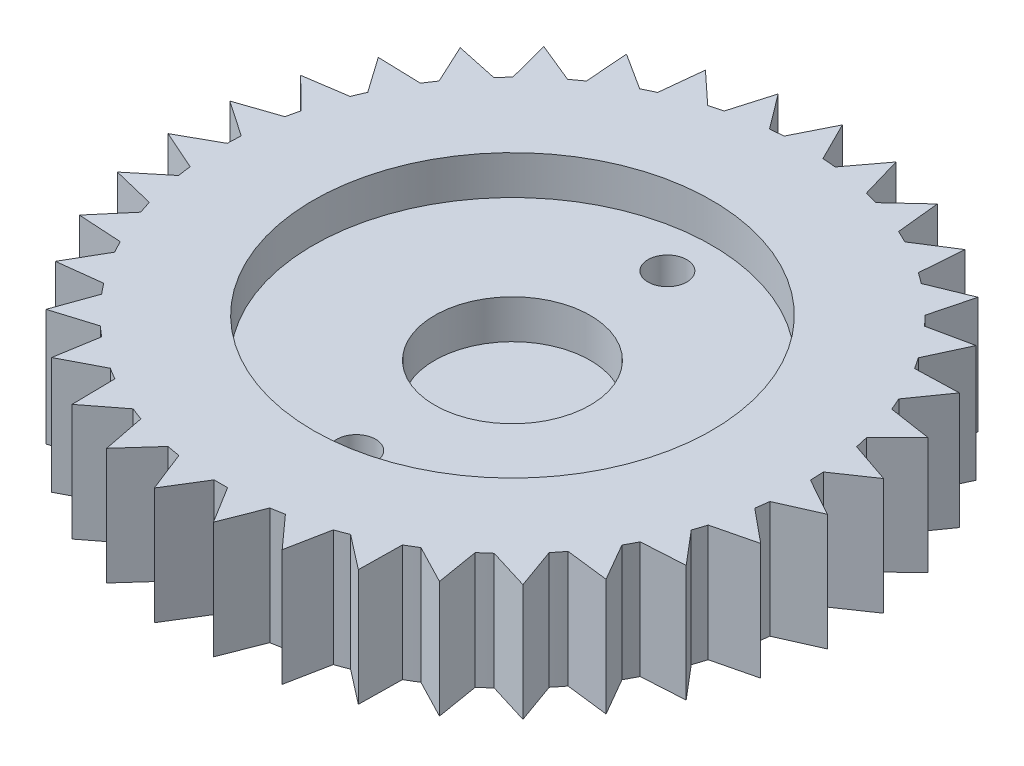
SolidWorks part; units mm, degrees
ref_plane "前视基准面" through (0, 0, 0) normal (0, 0, 1) x (1, 0, 0)
ref_plane "上视基准面" through (0, 0, 0) normal (0, 1, 0) x (1, 0, 0)
ref_plane "右视基准面" through (0, 0, 0) normal (1, 0, 0) x (0, 0, -1)
sketch "草图1" plane through (0, 0, 0) normal (0, 1, 0) x (1, 0, 0)
  circle A0 centre (0, 0) radius 15
  dimension "D1" = 30
extrude "凸台-拉伸1" add sketch "草图1" along normal blind 6
sketch "草图2" plane through (0, 6, 0) normal (0, 1, 0) x (1, 0, 0)
  line L0 (0, 16.9666) -> (-1, 14.9666)
  line L2 (1, 14.9666) -> (0, 16.9666)
  line L3 (0, 18.4375) -> (0, 11.2196) construction
  line L4 (-1, 14.9666) -> (-1, 14.9408)
  line L5 (-1, 14.9408) -> (1, 14.9408)
  line L6 (1, 14.9408) -> (1, 14.9666)
  line L7 (3.6563, 14.5476) -> (3.0295, 16.694)
  line L8 (3.0295, 16.694) -> (1.6885, 14.9047)
  line L9 (1.6885, 14.9047) -> (1.6838, 14.8792)
  line L10 (3.6517, 14.5221) -> (3.6563, 14.5476)
  line L11 (1.6838, 14.8792) -> (3.6517, 14.5221)
  line L12 (6.1951, 13.6609) -> (5.9616, 15.8848)
  line L13 (5.9616, 15.8848) -> (4.3227, 14.3637)
  line L14 (4.3227, 14.3637) -> (4.3136, 14.3394)
  line L15 (6.186, 13.6367) -> (6.1951, 13.6609)
  line L16 (4.3136, 14.3394) -> (6.186, 13.6367)
  line L17 (8.5348, 12.3352) -> (8.7022, 14.565)
  line L18 (8.7022, 14.565) -> (6.8179, 13.361)
  line L19 (6.8179, 13.361) -> (6.8047, 13.3388)
  line L20 (8.5216, 12.313) -> (8.5348, 12.3352)
  line L21 (6.8047, 13.3388) -> (8.5216, 12.313)
  line L22 (10.6002, 10.613) -> (11.163, 12.7771)
  line L23 (11.163, 12.7771) -> (9.0941, 11.9289)
  line L24 (9.0941, 11.9289) -> (9.077, 11.9094)
  line L25 (10.5832, 10.5935) -> (10.6002, 10.613)
  line L26 (9.077, 11.9094) -> (10.5832, 10.5935)
  line L27 (12.3249, 8.5497) -> (13.265, 10.5785)
  line L28 (13.265, 10.5785) -> (11.0779, 10.1134)
  line L29 (11.0779, 10.1134) -> (11.0577, 10.0973)
  line L30 (12.3047, 8.5336) -> (12.3249, 8.5497)
  line L31 (11.0577, 10.0973) -> (12.3047, 8.5336)
  line L32 (13.6534, 6.2116) -> (14.9407, 8.04)
  line L33 (14.9407, 8.04) -> (12.7057, 7.9728)
  line L34 (12.7057, 7.9728) -> (12.6829, 7.9606)
  line L35 (13.6306, 6.1994) -> (13.6534, 6.2116)
  line L36 (12.6829, 7.9606) -> (13.6306, 6.1994)
  line L37 (14.5431, 3.6739) -> (16.1362, 5.243)
  line L38 (16.1362, 5.243) -> (13.9251, 5.576)
  line L39 (13.9251, 5.576) -> (13.9005, 5.568)
  line L40 (14.5185, 3.6659) -> (14.5431, 3.6739)
  line L41 (13.9005, 5.568) -> (14.5185, 3.6659)
  line L42 (14.9654, 1.0181) -> (16.8131, 2.2775)
  line L43 (16.8131, 2.2775) -> (14.6969, 3)
  line L44 (14.6969, 3) -> (14.6713, 2.9965)
  line L45 (14.9398, 1.0146) -> (14.9654, 1.0181)
  line L46 (14.6713, 2.9965) -> (14.9398, 1.0146)
  line L47 (14.9067, -1.6705) -> (16.9495, -0.7612)
  line L48 (16.9495, -0.7612) -> (14.9964, 0.3275)
  line L49 (14.9964, 0.3275) -> (14.9706, 0.3287)
  line L50 (14.8809, -1.6693) -> (14.9067, -1.6705)
  line L51 (14.9706, 0.3287) -> (14.8809, -1.6693)
  line L52 (14.3689, -4.3053) -> (16.5412, -3.7754)
  line L53 (16.5412, -3.7754) -> (14.8139, -2.3555)
  line L54 (14.8139, -2.3555) -> (14.7887, -2.3497)
  line L55 (14.3437, -4.2996) -> (14.3689, -4.3053)
  line L56 (14.7887, -2.3497) -> (14.3437, -4.2996)
  line L57 (13.3692, -6.8018) -> (15.6013, -6.6683)
  line L58 (15.6013, -6.6683) -> (14.1553, -4.9627)
  line L59 (14.1553, -4.9627) -> (14.1315, -4.9526)
  line L60 (13.3454, -6.7916) -> (13.3692, -6.8018)
  line L61 (14.1315, -4.9526) -> (13.3454, -6.7916)
  line L62 (11.9399, -9.0796) -> (14.1599, -9.3469)
  line L63 (14.1599, -9.3469) -> (13.0416, -7.4105)
  line L64 (13.0416, -7.4105) -> (13.0201, -7.3963)
  line L65 (11.9183, -9.0654) -> (11.9399, -9.0796)
  line L66 (13.0201, -7.3963) -> (11.9183, -9.0654)
  line L67 (10.1267, -11.0657) -> (12.2634, -11.725)
  line L68 (12.2634, -11.725) -> (11.5089, -9.6201)
  line L69 (11.5089, -9.6201) -> (11.4902, -9.6022)
  line L70 (10.1081, -11.0478) -> (10.1267, -11.0657)
  line L71 (11.4902, -9.6022) -> (10.1081, -11.0478)
  line L72 (7.9881, -12.696) -> (9.9727, -13.7263)
  line L73 (9.9727, -13.7263) -> (9.6062, -11.5205)
  line L74 (9.6062, -11.5205) -> (9.591, -11.4996)
  line L75 (7.9729, -12.6751) -> (7.9881, -12.696)
  line L76 (9.591, -11.4996) -> (7.9729, -12.6751)
  line L77 (5.5928, -13.9184) -> (7.3615, -15.2864)
  line L78 (7.3615, -15.2864) -> (7.3947, -13.0506)
  line L79 (7.3947, -13.0506) -> (7.3835, -13.0273)
  line L80 (5.5816, -13.8951) -> (5.5928, -13.9184)
  line L81 (7.3835, -13.0273) -> (5.5816, -13.8951)
  line L82 (3.0177, -14.6933) -> (4.5137, -16.3552)
  line L83 (4.5137, -16.3552) -> (4.9456, -14.1612)
  line L84 (4.9456, -14.1612) -> (4.9388, -14.1363)
  line L85 (3.0108, -14.6684) -> (3.0177, -14.6933)
  line L86 (4.9388, -14.1363) -> (3.0108, -14.6684)
  line L87 (0.3456, -14.996) -> (1.5209, -16.8983)
  line L88 (1.5209, -16.8983) -> (2.3376, -14.8167)
  line L89 (2.3376, -14.8167) -> (2.3353, -14.791)
  line L90 (0.3433, -14.9703) -> (0.3456, -14.996)
  line L91 (2.3353, -14.791) -> (0.3433, -14.9703)
  line L92 (-2.3376, -14.8167) -> (-1.5209, -16.8983)
  line L93 (-1.5209, -16.8983) -> (-0.3456, -14.996)
  line L94 (-0.3456, -14.996) -> (-0.3433, -14.9703)
  line L95 (-2.3353, -14.791) -> (-2.3376, -14.8167)
  line L96 (-0.3433, -14.9703) -> (-2.3353, -14.791)
  line L97 (-4.9456, -14.1612) -> (-4.5137, -16.3552)
  line L98 (-4.5137, -16.3552) -> (-3.0177, -14.6933)
  line L99 (-3.0177, -14.6933) -> (-3.0108, -14.6684)
  line L100 (-4.9388, -14.1363) -> (-4.9456, -14.1612)
  line L101 (-3.0108, -14.6684) -> (-4.9388, -14.1363)
  line L102 (-7.3947, -13.0506) -> (-7.3615, -15.2864)
  line L103 (-7.3615, -15.2864) -> (-5.5928, -13.9184)
  line L104 (-5.5928, -13.9184) -> (-5.5816, -13.8951)
  line L105 (-7.3835, -13.0273) -> (-7.3947, -13.0506)
  line L106 (-5.5816, -13.8951) -> (-7.3835, -13.0273)
  line L107 (-9.6062, -11.5205) -> (-9.9727, -13.7263)
  line L108 (-9.9727, -13.7263) -> (-7.9881, -12.696)
  line L109 (-7.9881, -12.696) -> (-7.9729, -12.6751)
  line L110 (-9.591, -11.4996) -> (-9.6062, -11.5205)
  line L111 (-7.9729, -12.6751) -> (-9.591, -11.4996)
  line L112 (-11.5089, -9.6201) -> (-12.2634, -11.725)
  line L113 (-12.2634, -11.725) -> (-10.1267, -11.0657)
  line L114 (-10.1267, -11.0657) -> (-10.1081, -11.0478)
  line L115 (-11.4902, -9.6022) -> (-11.5089, -9.6201)
  line L116 (-10.1081, -11.0478) -> (-11.4902, -9.6022)
  line L117 (-13.0416, -7.4105) -> (-14.1599, -9.3469)
  line L118 (-14.1599, -9.3469) -> (-11.9399, -9.0796)
  line L119 (-11.9399, -9.0796) -> (-11.9183, -9.0654)
  line L120 (-13.0201, -7.3963) -> (-13.0416, -7.4105)
  line L121 (-11.9183, -9.0654) -> (-13.0201, -7.3963)
  line L122 (-14.1553, -4.9627) -> (-15.6013, -6.6683)
  line L123 (-15.6013, -6.6683) -> (-13.3692, -6.8018)
  line L124 (-13.3692, -6.8018) -> (-13.3454, -6.7916)
  line L125 (-14.1315, -4.9526) -> (-14.1553, -4.9627)
  line L126 (-13.3454, -6.7916) -> (-14.1315, -4.9526)
  line L127 (-14.8139, -2.3555) -> (-16.5412, -3.7754)
  line L128 (-16.5412, -3.7754) -> (-14.3689, -4.3053)
  line L129 (-14.3689, -4.3053) -> (-14.3437, -4.2996)
  line L130 (-14.7887, -2.3497) -> (-14.8139, -2.3555)
  line L131 (-14.3437, -4.2996) -> (-14.7887, -2.3497)
  line L132 (-14.9964, 0.3275) -> (-16.9495, -0.7612)
  line L133 (-16.9495, -0.7612) -> (-14.9067, -1.6705)
  line L134 (-14.9067, -1.6705) -> (-14.8809, -1.6693)
  line L135 (-14.9706, 0.3287) -> (-14.9964, 0.3275)
  line L136 (-14.8809, -1.6693) -> (-14.9706, 0.3287)
  line L137 (-14.6969, 3) -> (-16.8131, 2.2775)
  line L138 (-16.8131, 2.2775) -> (-14.9654, 1.0181)
  line L139 (-14.9654, 1.0181) -> (-14.9398, 1.0146)
  line L140 (-14.6713, 2.9965) -> (-14.6969, 3)
  line L141 (-14.9398, 1.0146) -> (-14.6713, 2.9965)
  line L142 (-13.9251, 5.576) -> (-16.1362, 5.243)
  line L143 (-16.1362, 5.243) -> (-14.5431, 3.6739)
  line L144 (-14.5431, 3.6739) -> (-14.5185, 3.6659)
  line L145 (-13.9005, 5.568) -> (-13.9251, 5.576)
  line L146 (-14.5185, 3.6659) -> (-13.9005, 5.568)
  line L147 (-12.7057, 7.9728) -> (-14.9407, 8.04)
  line L148 (-14.9407, 8.04) -> (-13.6534, 6.2116)
  line L149 (-13.6534, 6.2116) -> (-13.6306, 6.1994)
  line L150 (-12.6829, 7.9606) -> (-12.7057, 7.9728)
  line L151 (-13.6306, 6.1994) -> (-12.6829, 7.9606)
  line L152 (-11.0779, 10.1134) -> (-13.265, 10.5785)
  line L153 (-13.265, 10.5785) -> (-12.3249, 8.5497)
  line L154 (-12.3249, 8.5497) -> (-12.3047, 8.5336)
  line L155 (-11.0577, 10.0973) -> (-11.0779, 10.1134)
  line L156 (-12.3047, 8.5336) -> (-11.0577, 10.0973)
  line L157 (-9.0941, 11.9289) -> (-11.163, 12.7771)
  line L158 (-11.163, 12.7771) -> (-10.6002, 10.613)
  line L159 (-10.6002, 10.613) -> (-10.5832, 10.5935)
  line L160 (-9.077, 11.9094) -> (-9.0941, 11.9289)
  line L161 (-10.5832, 10.5935) -> (-9.077, 11.9094)
  line L162 (-6.8179, 13.361) -> (-8.7022, 14.565)
  line L163 (-8.7022, 14.565) -> (-8.5348, 12.3352)
  line L164 (-8.5348, 12.3352) -> (-8.5216, 12.313)
  line L165 (-6.8047, 13.3388) -> (-6.8179, 13.361)
  line L166 (-8.5216, 12.313) -> (-6.8047, 13.3388)
  line L167 (-4.3227, 14.3637) -> (-5.9616, 15.8848)
  line L168 (-5.9616, 15.8848) -> (-6.1951, 13.6609)
  line L169 (-6.1951, 13.6609) -> (-6.186, 13.6367)
  line L170 (-4.3136, 14.3394) -> (-4.3227, 14.3637)
  line L171 (-6.186, 13.6367) -> (-4.3136, 14.3394)
  line L172 (-1.6885, 14.9047) -> (-3.0295, 16.694)
  line L173 (-3.0295, 16.694) -> (-3.6563, 14.5476)
  line L174 (-3.6563, 14.5476) -> (-3.6517, 14.5221)
  line L175 (-1.6838, 14.8792) -> (-1.6885, 14.9047)
  line L176 (-3.6517, 14.5221) -> (-1.6838, 14.8792)
  circle A0 centre (0, 0) radius 15 construction
  point P182 (0, 0)
  dimension "D1" = 2
  dimension "D2" = 35
  dimension "D3" = 1
extrude "凸台-拉伸2" add sketch "草图2" against normal blind 6
sketch "草图3" plane through (0, 6, 0) normal (0, 1, 0) x (1, 0, 0)
  line L0 (0, 23.2168) -> (0, -25.1773) construction
  circle A0 centre (0, 7.9666) radius 1
  circle A1 centre (0, -8.0334) radius 1
  dimension "D3" = 2
  dimension "D4" = 2
  dimension "D1" = 9
  dimension "D2" = 16
extrude "切除-拉伸1" cut sketch "草图3" against normal blind 6
sketch "草图4" plane through (0, 6, 0) normal (0, 1, 0) x (1, 0, 0)
  circle A0 centre (0, 0) radius 10.25
  dimension "D1" = 20.5
extrude "切除-拉伸2" cut sketch "草图4" against normal blind 2
sketch "草图5" plane through (0, 4, 0) normal (0, 1, 0) x (1, 0, 0)
  circle A0 centre (0, 0) radius 4
  dimension "D1" = 8
extrude "切除-拉伸3" cut sketch "草图5" against normal blind 2
